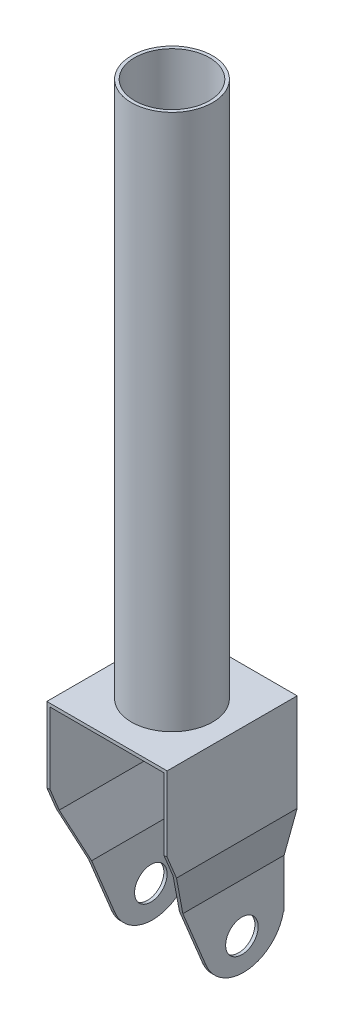
SolidWorks part; units mm, degrees
material "Aleación 1060"
ref_plane "Alzado" through (0, 0, 0) normal (0, 0, 1) x (1, 0, 0)
ref_plane "Planta" through (0, 0, 0) normal (0, 1, 0) x (1, 0, 0)
ref_plane "Vista lateral" through (0, 0, 0) normal (1, 0, 0) x (0, 0, -1)
sketch "Croquis1" plane through (0, 0, 0) normal (0, 1, 0) x (1, 0, 0)
  circle A0 centre (0, 0) radius 12.5
  dimension "D1" = 25
extrude "Saliente-Extruir1" add sketch "Croquis1" along normal blind 165
sketch "Croquis2" plane through (0, 165, 0) normal (0, 1, 0) x (1, 0, 0)
  circle A0 centre (0, 0) radius 11.5
  circle A1 centre (0, 0) radius 12.5 construction
  dimension "D1" = 1
extrude "Cortar-Extruir1" cut sketch "Croquis2" against normal through all
sketch "Croquis4" plane through (0, 0, 0) normal (0, 0, 1) x (1, 0, 0)
  line L0 (-18.5, 0) -> (18.5, 0)
  line L1 (-18.5, 0) -> (-18.5, -30)
  line L2 (14.5, -44.4568) -> (14.5, -69.4568)
  line L3 (-18.5, -30) -> (-14.5, -44.4568)
  line L4 (18.5, -30) -> (14.5, -44.4568)
  line L5 (-14.5, -44.4568) -> (-14.5, -69.4568)
  line L6 (18.5, 0) -> (18.5, -30)
  dimension "D3" = 30
  dimension "D5" = 15
  dimension "D7" = 25
extrude "Extruir-Lámina1" add sketch "Croquis4" along normal blind 20 thin
mirror "Simetría1" about plane through (0, 0, 0) normal (0, 0, 1) of "Extruir-Lámina1"
sketch "Croquis5" plane through (-14.5, 0, 0) normal (-1, 0, 0) x (0, 0, 1)
  line L0 (-20, -59.4568) -> (-7, -59.4568)
  line L1 (-20, -69.4568) -> (-20, -44.4568) construction
  line L2 (-7, -69.4568) -> (-7, -59.4568)
  line L3 (20, -69.4568) -> (-20, -69.4568) construction
  line L4 (20, -23) -> (4.0585, -61.7161)
  line L5 (20, -30) -> (20, 0) construction
  line L6 (20, -23) -> (20, -69.4568)
  line L7 (20, -69.4568) -> (-20, -69.4568)
  line L8 (-20, -69.4568) -> (-20, -59.4568)
  circle A0 centre (-7, -59.4568) radius 5
  arc A1 (-19.7474, -59.4568) -> (4.0585, -61.7161) centre (-7.5, -56.9568) ccw
  point P14 (-20, -56.9568)
  line M5 (20, -44.4568) -> (-20, -44.4568)
  line M6 (-20, -44.4568) -> (-20, -69.4568)
  line M7 (-20, -69.4568) -> (20, -69.4568)
  line M8 (20, -69.4568) -> (20, -44.4568)
  dimension "D3" = 25
  dimension "D1" = 13
  dimension "D2" = 10
extrude "Cortar-Extruir4" cut sketch "Croquis5" against normal through all both and the other way through all contours L6 L4 M5 | A1 L2 L4 M7 M8 M5 | A1 L0 M6 M7 | L0 A0 L2 | L2 A0 L0
sketch3d "Croquis3D5"
  point P0 (-0.7632, 108.0756, -12.4767)
ref_plane "Plano5" through (-0.1849, 0, -12.4852) normal (-0.0148, 0, -0.9999) x (-0.9999, 0, 0.0148)
sketch "Croquis6" plane through (-0.1849, 0, -12.4852) normal (-0.0148, 0, -0.9999) x (-0.9999, 0, 0.0148)
  circle A0 centre (0.8481, 108.6003) radius 2.9997
extrude "Cortar-Extruir5" cut sketch "Croquis6" against normal mid plane 10
